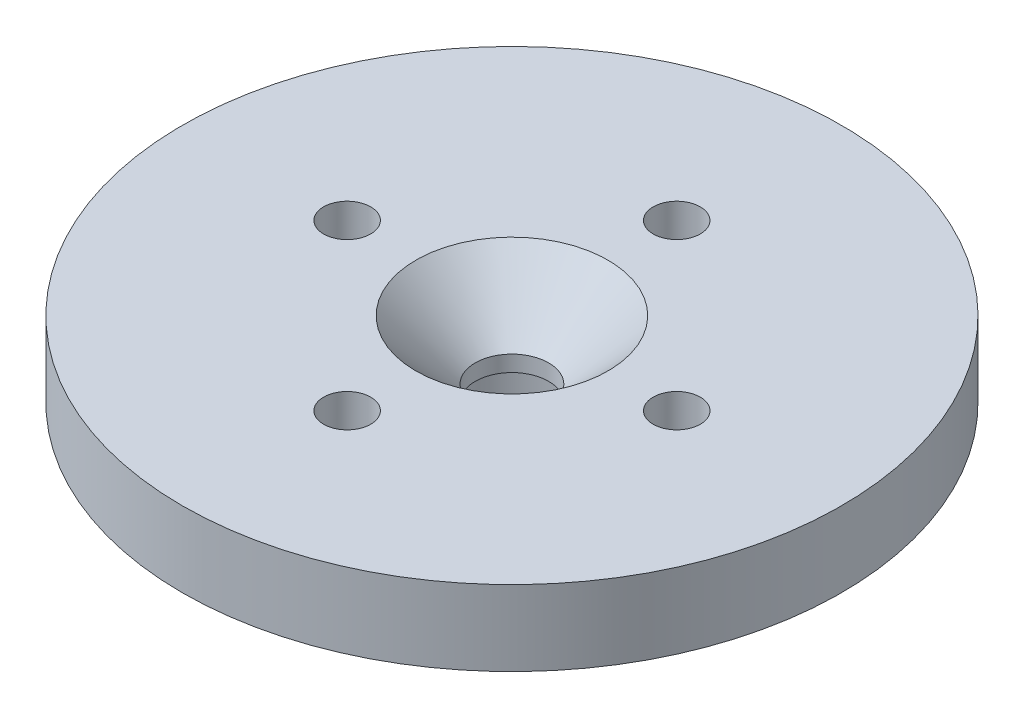
SolidWorks part; units mm, degrees
ref_plane "Front Plane" through (0, 0, 0) normal (0, 0, 1) x (1, 0, 0)
ref_plane "Top Plane" through (0, 0, 0) normal (0, 1, 0) x (1, 0, 0)
ref_plane "Right Plane" through (0, 0, 0) normal (1, 0, 0) x (0, 0, -1)
sketch "Sketch1" plane through (0, 0, 0) normal (0, 1, 0) x (1, 0, 0)
  circle A0 centre (0, 0) radius 17.5
  dimension "D1" = 35
extrude "Boss-Extrude1" add sketch "Sketch1" along normal blind 4
sketch "Sketch2" plane through (0, 0, 0) normal (0, -1, 0) x (1, 0, 0)
  circle A0 centre (0, 0) radius 4
  circle A1 centre (0, 0) radius 5
extrude "Boss-Extrude2" add sketch "Sketch2" along normal blind 6.9
sketch "Sketch3" plane through (0, 0, 0) normal (0, -1, 0) x (1, 0, 0)
  line L0 (0, 17.5) -> (0, 0) construction
  line L1 (0, 0) -> (0, -17.5) construction
  line L2 (-17.5, 0) -> (0, 0) construction
  line L3 (0, 0) -> (17.5, 0) construction
  circle A1 centre (0, 0) radius 17.5 construction
  circle A2 centre (-8.75, 0) radius 1.25
  circle A3 centre (8.75, 0) radius 1.25
extrude "Cut-Extrude1" cut sketch "Sketch3" against normal blind 6.9
hole_wizard "CSK for M3.5 Flat Head Machine Screw1" positions "Sketch5" profile "Sketch4" countersink size "M3.5" standard "ANSI Metric" end condition through all
sketch "Sketch5" plane through (0, 4, 0) normal (0, 1, 0) x (1, 0, 0)
  point P0 (0, 0)
sketch "Sketch4" plane through (0, 4, 0) normal (1, 0, 0) x (0, 0, 1)
  line L0 (0, 0) -> (0, 10.9)
  line L1 (0, 10.9) -> (1.95, 10.9)
  line L2 (1.95, 10.9) -> (1.95, 3.15)
  line L3 (1.95, 3.15) -> (5.1, 0)
  line L5 (5.1, 0) -> (0, 0)
  line L6 (-1.95, 3.15) -> (-5.1, 0) construction
  line L11 (0, -6.35) -> (0, 107.95) construction
  dimension "Thru Hole Dia." = 3.9
  dimension "Thru Hole Depth" = 10.9
  dimension "Near C'Sink Dia." = 10.2
  dimension "Near C'Sink Angle" = 90
sketch "Sketch6" plane through (0, 0, 0) normal (0, -1, 0) x (1, 0, 0)
  line L0 (0, 17.5) -> (0, 0) construction
  line L1 (0, 0) -> (0, -17.5) construction
  circle A0 centre (0, 0) radius 17.5 construction
  circle A1 centre (0, 8.75) radius 1.25
  circle A2 centre (0, -8.75) radius 1.25
extrude "Cut-Extrude2" cut sketch "Sketch6" against normal blind 6.9
